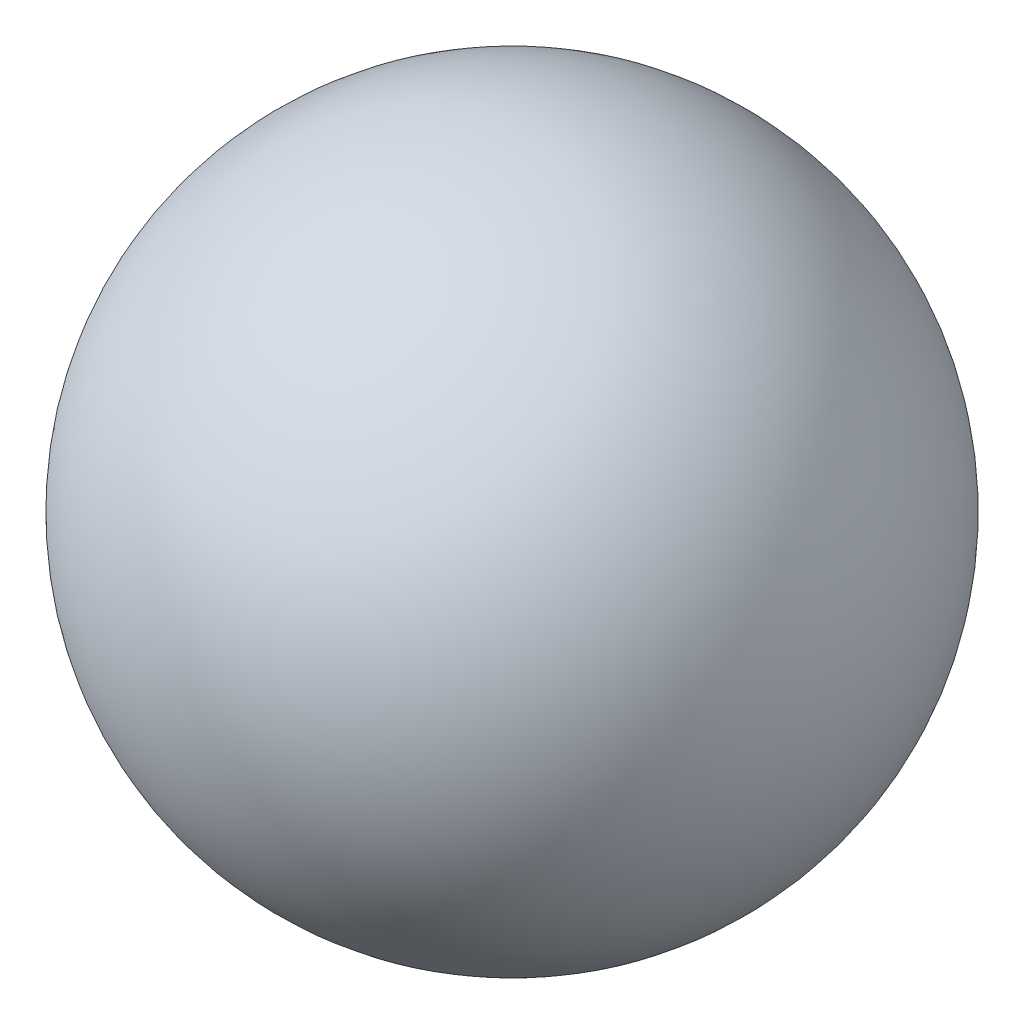
SolidWorks part; units mm, degrees
ref_plane "Front Plane" through (0, 0, 0) normal (0, 0, 1) x (1, 0, 0)
ref_plane "Top Plane" through (0, 0, 0) normal (0, 1, 0) x (1, 0, 0)
ref_plane "Right Plane" through (0, 0, 0) normal (1, 0, 0) x (0, 0, -1)
sketch "Sketch1" plane through (0, 0, 0) normal (0, 0, 1) x (1, 0, 0)
  line L0 (1.5465, 41.6754) -> (1.5465, -38.3246)
  arc A0 (1.5465, 41.6754) -> (1.5465, -38.3246) centre (1.5465, 1.6754) cw
revolve "Revolve1" add sketch "Sketch1" angle 360 about L0
